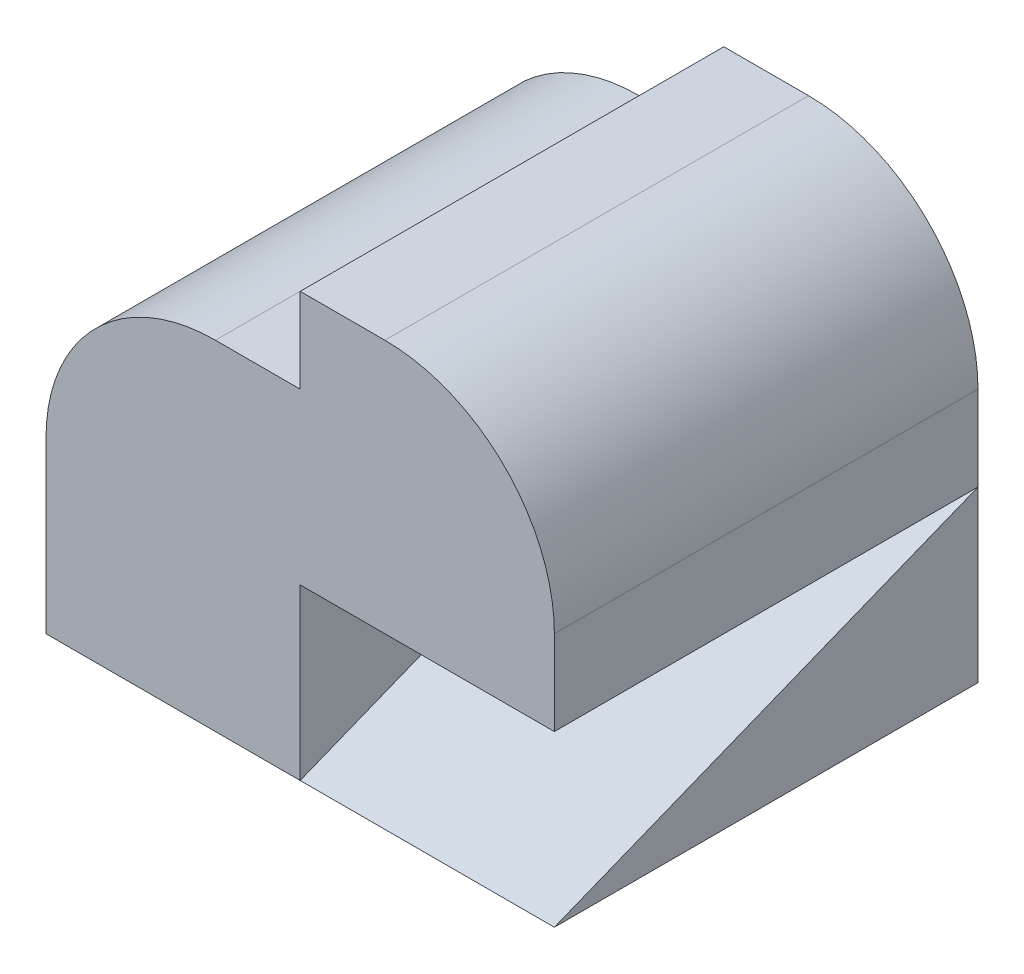
SolidWorks part; units mm, degrees
ref_plane "Front Plane" through (0, 0, 0) normal (0, 0, 1) x (1, 0, 0)
ref_plane "Top Plane" through (0, 0, 0) normal (0, 1, 0) x (1, 0, 0)
ref_plane "Right Plane" through (0, 0, 0) normal (1, 0, 0) x (0, 0, -1)
sketch "Sketch1" plane through (0, 0, 0) normal (0, 0, 1) x (1, 0, 0)
  line L0 (-15, 0) -> (0, 0)
  line L1 (0, 0) -> (0, 20)
  line L2 (0, 20) -> (-5, 20)
  line L3 (-15, 0) -> (-15, 10)
  arc A0 (-15, 10) -> (-5, 20) centre (-5, 10) cw
  dimension "D1" = 5
  dimension "D2" = 10
  dimension "D3" = 20
extrude "Boss-Extrude1" add sketch "Sketch1" along normal blind 25
sketch "Sketch2" plane through (0, 0, 25) normal (0, 0, 1) x (1, 0, 0)
  line L0 (0, 10) -> (0, 25)
  line L2 (0, 10) -> (15, 10)
  line L3 (15, 10) -> (15, 15)
  line L4 (0, 25) -> (5, 25)
  line L5 (0, 0) -> (0, 20) construction
  arc A0 (15, 15) -> (5, 25) centre (5, 15) ccw
  dimension "D1" = 5
  dimension "D2" = 10
  dimension "D3" = 5
  dimension "D4" = 15
extrude "Boss-Extrude3" add sketch "Sketch2" against normal blind 25
sketch "Sketch3" plane through (0, 0, 0) normal (1, 0, 0) x (0, 0, -1)
  line L0 (-25, 0) -> (0, 10)
  line L1 (0, 10) -> (0, 0)
  line L2 (0, 0) -> (-25, 0)
extrude "Boss-Extrude5" add sketch "Sketch3" along normal blind 15 separate body
